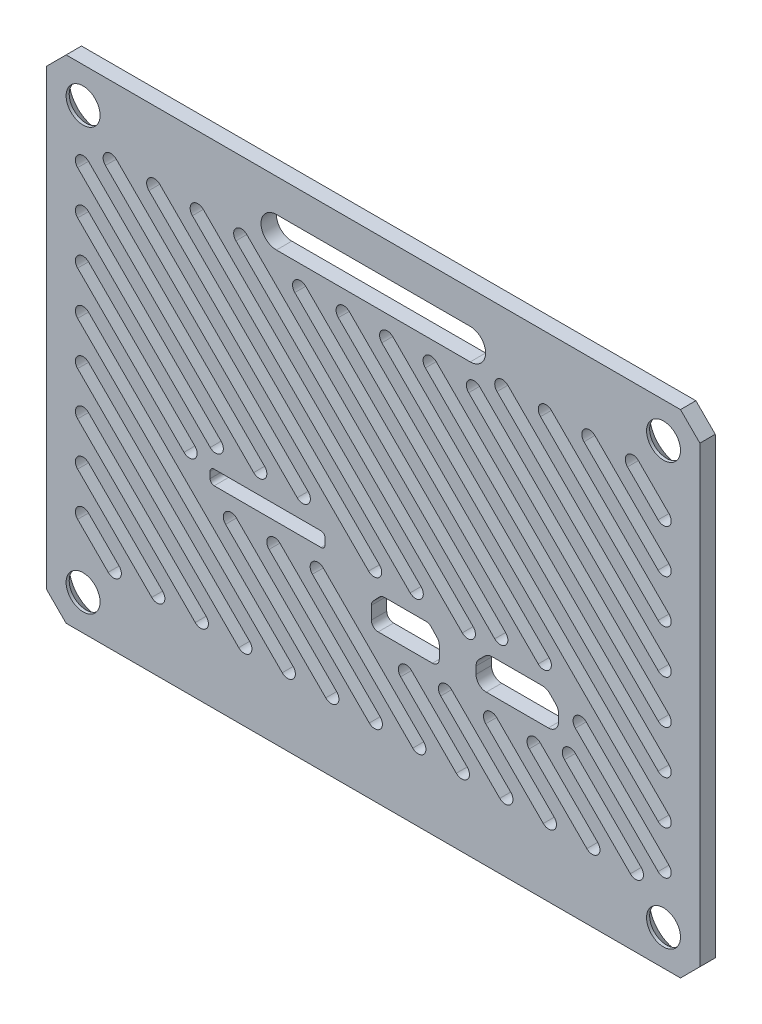
SolidWorks part; units mm, degrees
ref_plane "Front Plane" through (0, 0, 0) normal (0, 0, 1) x (1, 0, 0)
ref_plane "Top Plane" through (0, 0, 0) normal (0, 1, 0) x (1, 0, 0)
ref_plane "Right Plane" through (0, 0, 0) normal (1, 0, 0) x (0, 0, -1)
sketch "Sketch1" plane through (0, 0, 0) normal (0, 0, 1) x (1, 0, 0)
  line L1 (0, 0) -> (67.4, 0)
  line L2 (0, 0) -> (0, 50.8)
  line L3 (0, 50.8) -> (67.4, 50.8)
  line L4 (67.4, 0) -> (67.4, 50.8)
  dimension "D1" = 67.4
  dimension "D2" = 50.8
extrude "Boss-Extrude1" add sketch "Sketch1" along normal blind 1.5875
chamfer "Chamfer1" distance 2 angle 45 4 edges at (0, 0, 0.7937) (0, 50.8, 0.7937) (67.4, 0, 0.7937) (67.4, 50.8, 0.7937)
sketch "Sketch3" plane through (0, 0, 0) normal (0, 0, -1) x (-1, 0, 0)
  line L0 (-67.4, 25.4) -> (0, 25.4) construction
  line L1 (-67.4, 2) -> (-67.4, 48.8) construction
  line L2 (0, 48.8) -> (0, 2) construction
  line L3 (-63.65, 47.15) -> (-3.75, 47.15) construction
  line L4 (-65.4, 50.8) -> (-2, 50.8) construction
  line L5 (-33.7, 50.8) -> (-33.7, 0) construction
  line L6 (-2, 0) -> (-65.4, 0) construction
  line L7 (-3.75, 47.15) -> (-3.75, 3.65) construction
  circle A0 centre (-63.65, 47.15) radius 1.75
  circle A1 centre (-3.75, 47.15) radius 1.75
  circle A2 centre (-3.75, 3.65) radius 1.75
  circle A3 centre (-63.65, 3.65) radius 1.75
  arc A4 (-64.525, 4.6114) -> (-62.775, 4.6114) centre (-63.65, 3.65) ccw construction
  point P20 (-33.7, 47.15)
  point P21 (-3.75, 25.4)
  dimension "D1" = 3.5
extrude "Cut-Extrude2" cut sketch "Sketch3" against normal through all
chamfer "Chamfer2" distance 1.27 angle 45 4 edges at (2, 3.65, 0) (61.9, 3.65, 0) (2, 47.15, 0) (61.9, 47.15, 0)
sketch "Sketch5" plane through (0, 0, 0) normal (0, 0, -1) x (-1, 0, 0)
  line L0 (-43.7, 45.8) -> (-23.7, 45.8) construction
  line L1 (-43.7, 47.3875) -> (-23.7, 47.3875)
  line L2 (-43.7, 44.2125) -> (-23.7, 44.2125)
  line L3 (-33.7, 50.8) -> (-33.7, 45.8) construction
  line L5 (-65.4, 50.8) -> (-2, 50.8) construction
  arc A0 (-43.7, 47.3875) -> (-43.7, 44.2125) centre (-43.7, 45.8) ccw
  arc A1 (-23.7, 44.2125) -> (-23.7, 47.3875) centre (-23.7, 45.8) ccw
  point P2 (-33.7, 45.8)
  dimension "D1" = 1.5875
  dimension "D2" = 20
  dimension "D3" = 5
extrude "Cut-Extrude4" cut sketch "Sketch5" against normal through all
sketch "Sketch6" plane through (0, 0, 0) normal (0, 0, -1) x (-1, 0, 0)
  line L0 (-45.3591, 16.0375) -> (-51.7591, 16.0375) construction
  line L1 (-18.2758, 20.1823) -> (-21.3912, 20.1823) construction
  line L2 (-44.8091, 17.2375) -> (-44.8091, 16.6375) construction
  line L3 (-19.2565, 21.1623) -> (-19.4565, 21.1623) construction
  line L4 (-44.9701, 17.7229) -> (-45.5737, 18.3264) construction
  line L5 (-17.1065, 20.2823) -> (-17.1065, 21.2773) construction
  line L6 (-28.4665, 21.0123) -> (-28.4665, 20.2223) construction
  line L7 (-52.3091, 16.6375) -> (-52.3091, 16.5875) construction
  line L8 (-17.2765, 19.9283) -> (-28.2965, 19.9283)
  line L9 (-28.7205, 20.3523) -> (-28.7205, 20.9923)
  line L10 (-51.5444, 18.3264) -> (-52.148, 17.7229) construction
  line L11 (-17.2765, 21.4163) -> (-28.2965, 21.4163)
  line L12 (-51.0591, 18.4875) -> (-48.5691, 18.4875) construction
  line L13 (-45.3591, 16.0375) -> (-51.7591, 16.0375) construction
  line L14 (-45.3591, 15.5295) -> (-51.7591, 15.5295)
  line L15 (-44.8091, 17.3339) -> (-44.8091, 16.5875) construction
  line L16 (-52.8171, 17.3339) -> (-52.8171, 16.5875)
  line L17 (-44.9701, 17.7229) -> (-45.5737, 18.3264) construction
  line L18 (-51.9036, 18.6856) -> (-52.5072, 18.0821)
  line L19 (-51.1555, 18.9955) -> (-45.9626, 18.9955)
  line L20 (-52.3091, 17.3339) -> (-52.3091, 16.5875) construction
  line L21 (-44.6109, 18.0821) -> (-45.2145, 18.6856)
  line L22 (-44.3011, 17.3339) -> (-44.3011, 16.5875)
  line L23 (-51.5444, 18.3264) -> (-52.148, 17.7229) construction
  line L24 (-16.8525, 20.3523) -> (-16.8525, 20.9923)
  line L25 (-51.1555, 18.4875) -> (-45.9626, 18.4875) construction
  line L39 (-34.2021, 15.5875) -> (-39.8021, 15.5875) construction
  line L40 (-33.7521, 17.3577) -> (-33.7521, 16.0375) construction
  line L41 (-34.52, 18.3471) -> (-33.8755, 17.6673) construction
  line L42 (-36.8421, 18.4875) -> (-34.8466, 18.4875) construction
  line L43 (-40.2521, 16.0375) -> (-40.2521, 17.3577) construction
  line L44 (-40.1286, 17.6673) -> (-39.4841, 18.3471) construction
  line L45 (-39.1576, 18.4875) -> (-37.1621, 18.4875) construction
  line L46 (-34.2021, 15.5875) -> (-39.8021, 15.5875) construction
  line L47 (-33.7521, 17.3577) -> (-33.7521, 16.0375) construction
  line L48 (-34.52, 18.3471) -> (-33.8755, 17.6673) construction
  line L49 (-36.8421, 18.4875) -> (-34.8466, 18.4875) construction
  line L50 (-40.2521, 16.0375) -> (-40.2521, 17.3577) construction
  line L51 (-40.1286, 17.6673) -> (-39.4841, 18.3471) construction
  line L52 (-39.1576, 18.4875) -> (-37.1621, 18.4875) construction
  line L53 (-36.8421, 18.4875) -> (-37.1621, 18.4875) construction
  line L54 (-34.2021, 15.3335) -> (-39.8021, 15.3335)
  line L55 (-40.5061, 16.0375) -> (-40.5061, 17.3577)
  line L56 (-40.313, 17.8421) -> (-39.6685, 18.5219)
  line L57 (-39.1576, 18.7415) -> (-37.1621, 18.7415)
  line L58 (-36.8421, 18.7415) -> (-37.1621, 18.7415)
  line L59 (-36.8421, 18.7415) -> (-34.8466, 18.7415)
  line L60 (-34.3357, 18.5219) -> (-33.6912, 17.8421)
  line L61 (-33.4981, 17.3577) -> (-33.4981, 16.0375)
  line L193 (-17.1065, 20.3523) -> (-17.1065, 20.9923) construction
  line L195 (-17.2765, 20.1823) -> (-28.2965, 20.1823) construction
  line L199 (-28.4665, 20.3523) -> (-28.4665, 20.9923) construction
  line L200 (-17.2765, 21.1623) -> (-28.2965, 21.1623) construction
  arc A0 (-45.3591, 16.0375) -> (-44.8091, 16.5875) centre (-45.3591, 16.5875) ccw construction
  arc A1 (-44.8091, 17.3339) -> (-44.9701, 17.7229) centre (-45.3591, 17.3339) ccw construction
  arc A2 (-45.5737, 18.3264) -> (-45.9626, 18.4875) centre (-45.9626, 17.9375) ccw construction
  arc A3 (-52.3091, 16.5875) -> (-51.7591, 16.0375) centre (-51.7591, 16.5875) ccw construction
  arc A4 (-52.148, 17.7229) -> (-52.3091, 17.3339) centre (-51.7591, 17.3339) ccw construction
  arc A5 (-51.1555, 18.4875) -> (-51.5444, 18.3264) centre (-51.1555, 17.9375) ccw construction
  arc A6 (-45.3591, 16.0375) -> (-44.8091, 16.5875) centre (-45.3591, 16.5875) ccw construction
  arc A7 (-44.8091, 17.3339) -> (-44.9701, 17.7229) centre (-45.3591, 17.3339) ccw construction
  arc A8 (-45.5737, 18.3264) -> (-45.9626, 18.4875) centre (-45.9626, 17.9375) ccw construction
  arc A9 (-52.3091, 16.5875) -> (-51.7591, 16.0375) centre (-51.7591, 16.5875) ccw construction
  arc A10 (-52.148, 17.7229) -> (-52.3091, 17.3339) centre (-51.7591, 17.3339) ccw construction
  arc A11 (-51.1555, 18.4875) -> (-51.5444, 18.3264) centre (-51.1555, 17.9375) ccw construction
  arc A12 (-52.8171, 16.5875) -> (-51.7591, 15.5295) centre (-51.7591, 16.5875) ccw
  arc A13 (-52.5072, 18.0821) -> (-52.8171, 17.3339) centre (-51.7591, 17.3339) ccw
  arc A14 (-51.1555, 18.9955) -> (-51.9036, 18.6856) centre (-51.1555, 17.9375) ccw
  arc A15 (-45.2145, 18.6856) -> (-45.9626, 18.9955) centre (-45.9626, 17.9375) ccw
  arc A16 (-44.3011, 17.3339) -> (-44.6109, 18.0821) centre (-45.3591, 17.3339) ccw
  arc A17 (-45.3591, 15.5295) -> (-44.3011, 16.5875) centre (-45.3591, 16.5875) ccw
  arc A18 (-34.2021, 15.5875) -> (-33.7521, 16.0375) centre (-34.2021, 16.0375) ccw construction
  arc A19 (-33.7521, 17.3577) -> (-33.8755, 17.6673) centre (-34.2021, 17.3577) ccw construction
  arc A20 (-34.52, 18.3471) -> (-34.8466, 18.4875) centre (-34.8466, 18.0375) ccw construction
  arc A21 (-40.2521, 16.0375) -> (-39.8021, 15.5875) centre (-39.8021, 16.0375) ccw construction
  arc A22 (-40.1286, 17.6673) -> (-40.2521, 17.3577) centre (-39.8021, 17.3577) ccw construction
  arc A23 (-39.1576, 18.4875) -> (-39.4841, 18.3471) centre (-39.1576, 18.0375) ccw construction
  arc A24 (-34.2021, 15.5875) -> (-33.7521, 16.0375) centre (-34.2021, 16.0375) ccw construction
  arc A25 (-33.7521, 17.3577) -> (-33.8755, 17.6673) centre (-34.2021, 17.3577) ccw construction
  arc A26 (-34.52, 18.3471) -> (-34.8466, 18.4875) centre (-34.8466, 18.0375) ccw construction
  arc A27 (-40.2521, 16.0375) -> (-39.8021, 15.5875) centre (-39.8021, 16.0375) ccw construction
  arc A28 (-40.1286, 17.6673) -> (-40.2521, 17.3577) centre (-39.8021, 17.3577) ccw construction
  arc A29 (-39.1576, 18.4875) -> (-39.4841, 18.3471) centre (-39.1576, 18.0375) ccw construction
  arc A30 (-40.5061, 16.0375) -> (-39.8021, 15.3335) centre (-39.8021, 16.0375) ccw
  arc A31 (-40.313, 17.8421) -> (-40.5061, 17.3577) centre (-39.8021, 17.3577) ccw
  arc A32 (-39.1576, 18.7415) -> (-39.6685, 18.5219) centre (-39.1576, 18.0375) ccw
  arc A33 (-34.3357, 18.5219) -> (-34.8466, 18.7415) centre (-34.8466, 18.0375) ccw
  arc A34 (-33.4981, 17.3577) -> (-33.6912, 17.8421) centre (-34.2021, 17.3577) ccw
  arc A35 (-34.2021, 15.3335) -> (-33.4981, 16.0375) centre (-34.2021, 16.0375) ccw
  arc A36 (-28.7205, 20.3523) -> (-28.2965, 19.9283) centre (-28.2965, 20.3523) ccw
  arc A37 (-28.7205, 20.9923) -> (-28.2965, 21.4163) centre (-28.2965, 20.9923) cw
  arc A38 (-16.8525, 20.9923) -> (-17.2765, 21.4163) centre (-17.2765, 20.9923) ccw
  arc A39 (-17.2765, 19.9283) -> (-16.8525, 20.3523) centre (-17.2765, 20.3523) ccw
  arc A56 (-28.4665, 20.9923) -> (-28.2965, 21.1623) centre (-28.2965, 20.9923) cw construction
  arc A57 (-28.4665, 20.3523) -> (-28.2965, 20.1823) centre (-28.2965, 20.3523) ccw construction
  arc A58 (-17.1065, 20.9923) -> (-17.2765, 21.1623) centre (-17.2765, 20.9923) ccw construction
  arc A59 (-17.2765, 20.1823) -> (-17.1065, 20.3523) centre (-17.2765, 20.3523) ccw construction
  dimension "D3" = 0.254
  dimension "D5" = 0.17
  dimension "D1" = 0.508
  dimension "D2" = 0.254
extrude "Cut-Extrude5" cut sketch "Sketch6" against normal up to surface (1.5875 mm away) up to face at (33.7, 45.8, 1.5875)
sketch "Sketch7" plane through (0, 0, 0) normal (0, 0, -1) x (-1, 0, 0)
  line L0 (-3.75, 14.9388) -> (-11.3951, 7.2938) construction
  line L1 (-3.1887, 14.3776) -> (-10.8338, 6.7325)
  line L2 (-4.3113, 15.5001) -> (-11.9564, 7.855)
  line L3 (-14.724, 21.9254) -> (-3.75, 32.8994) construction
  line L4 (-28.2965, 18.4283) -> (-17.2765, 18.4283) construction
  line L5 (-15.3525, 20.3523) -> (-15.3525, 20.9923) construction
  line L7 (-17.2765, 22.9163) -> (-28.2965, 22.9163) construction
  line L8 (-30.2205, 20.9923) -> (-30.2205, 20.3523) construction
  line L9 (-28.2965, 19.9283) -> (-17.2765, 19.9283)
  line L10 (-2.9562, 6.5) -> (-64.4437, 6.5) construction
  line L11 (-2.9562, 6.5) -> (-2.9562, 44.3) construction
  line L12 (-2.9562, 44.3) -> (-64.4437, 44.3) construction
  line L13 (-64.4437, 6.5) -> (-64.4437, 44.3) construction
  line L14 (-60.8864, 44.3) -> (-50.65, 44.3) construction
  line L16 (-6.5136, 6.5) -> (-60.8864, 6.5) construction
  line L17 (-3.75, 10.4487) -> (-6.905, 7.2938) construction
  line L18 (-3.1887, 9.8875) -> (-6.3437, 6.7325)
  line L19 (-4.3113, 11.01) -> (-7.4662, 7.855)
  line L20 (-3.75, 19.429) -> (-15.8852, 7.2938) construction
  line L21 (-3.1887, 18.8677) -> (-15.324, 6.7325)
  line L22 (-4.3113, 19.9902) -> (-16.4465, 7.855)
  line L23 (-3.75, 23.9191) -> (-20.3754, 7.2938) construction
  line L24 (-3.1887, 23.3578) -> (-19.8141, 6.7325)
  line L25 (-4.3113, 24.4804) -> (-20.9366, 7.855)
  line L26 (-3.75, 28.4092) -> (-24.8655, 7.2938) construction
  line L27 (-3.1887, 27.848) -> (-24.3042, 6.7325)
  line L28 (-4.3113, 28.9705) -> (-25.4267, 7.855)
  line L29 (-19.0148, 17.6345) -> (-29.3556, 7.2938) construction
  line L30 (-18.4535, 17.0733) -> (-28.7943, 6.7325)
  line L31 (-19.5761, 18.1958) -> (-29.9169, 7.855)
  line L32 (-23.5049, 17.6345) -> (-33.8457, 7.2938) construction
  line L33 (-22.9437, 17.0733) -> (-33.2845, 6.7325)
  line L34 (-24.0662, 18.1958) -> (-34.407, 7.855)
  line L35 (-27.9761, 17.6535) -> (-38.3359, 7.2938) construction
  line L36 (-27.4148, 17.0922) -> (-37.7746, 6.7325)
  line L37 (-28.5374, 18.2148) -> (-38.8971, 7.855)
  line L38 (-3.75, 41.8796) -> (-21.9196, 23.71) construction
  line L39 (-3.1887, 41.3183) -> (-21.3583, 23.1488)
  line L40 (-4.3113, 42.4409) -> (-22.4808, 24.2713)
  line L41 (-37.08, 13.0397) -> (-42.826, 7.2938) construction
  line L42 (-36.5187, 12.4785) -> (-42.2647, 6.7325)
  line L43 (-37.6413, 13.601) -> (-43.3873, 7.855)
  line L44 (-6.6135, 43.5063) -> (-26.4097, 23.71) construction
  line L45 (-6.0522, 42.945) -> (-25.8484, 23.1488)
  line L46 (-7.1748, 44.0675) -> (-26.971, 24.2713)
  line L47 (-41.2158, 13.3941) -> (-47.3161, 7.2938) construction
  line L48 (-40.6546, 12.8328) -> (-46.7549, 6.7325)
  line L49 (-41.7771, 13.9553) -> (-47.8774, 7.855)
  line L50 (-45.8643, 13.2357) -> (-51.8062, 7.2938) construction
  line L51 (-45.303, 12.6745) -> (-51.245, 6.7325)
  line L52 (-46.4255, 13.797) -> (-52.3675, 7.855)
  line L53 (-11.1036, 43.5063) -> (-33.7733, 20.8365) construction
  line L54 (-10.5424, 42.945) -> (-33.2121, 20.2753)
  line L55 (-11.6649, 44.0675) -> (-34.3346, 21.3978)
  line L56 (-15.5937, 43.5063) -> (-38.0647, 21.0352) construction
  line L57 (-15.0325, 42.945) -> (-37.5035, 20.474)
  line L58 (-16.155, 44.0675) -> (-38.626, 21.5965)
  line L59 (-50.3544, 13.2357) -> (-56.2964, 7.2938) construction
  line L60 (-49.7931, 12.6745) -> (-55.7351, 6.7325)
  line L61 (-50.9156, 13.797) -> (-56.8576, 7.855)
  line L62 (-53.9922, 14.088) -> (-60.7865, 7.2938) construction
  line L63 (-53.4309, 13.5268) -> (-60.2252, 6.7325)
  line L64 (-54.5535, 14.6493) -> (-61.3478, 7.855)
  line L65 (-20.0839, 43.5063) -> (-43.4426, 20.1475) construction
  line L66 (-19.5226, 42.945) -> (-42.8814, 19.5862)
  line L67 (-20.6451, 44.0675) -> (-44.0039, 20.7087)
  line L68 (-26.1615, 41.9188) -> (-46.791, 21.2892) construction
  line L69 (-25.6002, 41.3575) -> (-46.2297, 20.728)
  line L70 (-26.7228, 42.48) -> (-47.3523, 21.8505)
  line L71 (-55.1084, 17.462) -> (-63.65, 8.9204) construction
  line L72 (-54.5471, 16.9008) -> (-63.0887, 8.3591)
  line L73 (-55.6696, 18.0233) -> (-64.2113, 9.4817)
  line L74 (-35.1418, 41.9188) -> (-63.65, 13.4105) construction
  line L75 (-34.5805, 41.3575) -> (-63.0887, 12.8492)
  line L76 (-35.703, 42.48) -> (-64.2113, 13.9718)
  line L77 (-28.7205, 20.9923) -> (-28.7205, 20.3523)
  line L78 (-5.3275, 8.8712) -> (-7.5725, 11.1163) construction
  line L79 (-7.5725, 11.1163) -> (-9.8176, 13.3614) construction
  line L80 (-9.8176, 13.3614) -> (-12.0627, 15.6064) construction
  line L81 (-12.0627, 15.6064) -> (-14.3077, 17.8515) construction
  line L82 (-15.2852, 22.4867) -> (-4.3113, 33.4606)
  line L83 (-14.1627, 21.3641) -> (-3.1887, 32.3381)
  line L84 (-17.2765, 21.4163) -> (-28.2965, 21.4163)
  line L85 (-16.8525, 20.3523) -> (-16.8525, 20.9923)
  line L86 (-28.2965, 19.9283) -> (-17.2765, 19.9283) construction
  line L87 (-28.7205, 20.9923) -> (-28.7205, 20.3523) construction
  line L88 (-17.2765, 21.4163) -> (-28.2965, 21.4163) construction
  line L89 (-16.8525, 20.3523) -> (-16.8525, 20.9923) construction
  line L90 (-3.75, 37.3895) -> (-17.4294, 23.71) construction
  line L91 (-3.1887, 36.8282) -> (-16.8682, 23.1488)
  line L92 (-4.3113, 37.9508) -> (-17.9907, 24.2713)
  line L93 (-38.3359, 7.2938) -> (-40.5809, 9.5388) construction
  line L94 (-47.3161, 7.2938) -> (-49.5612, 9.5388) construction
  line L95 (-51.8062, 7.2938) -> (-54.0513, 9.5388) construction
  line L96 (-56.2964, 7.2938) -> (-58.5414, 9.5388) construction
  line L97 (-5.3275, 8.8712) -> (-2.9562, 6.5) construction
  line L99 (-60.7865, 7.2938) -> (-63.0316, 9.5388) construction
  line L100 (-42.826, 7.2938) -> (-45.0711, 9.5388) construction
  line L101 (-33.8457, 7.2938) -> (-36.0908, 9.5388) construction
  line L102 (-29.3556, 7.2938) -> (-31.6007, 9.5388) construction
  line L103 (-23.7, 48.8875) -> (-43.7, 48.8875)
  line L104 (-43.7, 42.7125) -> (-23.7, 42.7125)
  line L105 (-23.7, 48.8875) -> (-43.7, 48.8875) construction
  line L106 (-43.7, 42.7125) -> (-23.7, 42.7125) construction
  line L107 (-34.8466, 20.2415) -> (-39.1576, 20.2415)
  line L108 (-40.757, 19.5539) -> (-41.4015, 18.8741)
  line L109 (-42.0061, 17.3577) -> (-42.0061, 16.0375)
  line L110 (-39.8021, 13.8335) -> (-34.2021, 13.8335)
  line L111 (-31.9981, 16.0375) -> (-31.9981, 17.3577)
  line L112 (-32.6026, 18.8741) -> (-33.2471, 19.5539)
  line L113 (-34.8466, 20.2415) -> (-39.1576, 20.2415) construction
  line L114 (-40.757, 19.5539) -> (-41.4015, 18.8741) construction
  line L115 (-42.0061, 17.3577) -> (-42.0061, 16.0375) construction
  line L116 (-39.8021, 13.8335) -> (-34.2021, 13.8335) construction
  line L117 (-31.9981, 16.0375) -> (-31.9981, 17.3577) construction
  line L118 (-32.6026, 18.8741) -> (-33.2471, 19.5539) construction
  line L119 (-42.8011, 16.5875) -> (-42.8011, 17.3339)
  line L120 (-43.5503, 19.1427) -> (-44.1538, 19.7463)
  line L121 (-45.9626, 20.4955) -> (-51.1555, 20.4955)
  line L122 (-52.9643, 19.7463) -> (-53.5678, 19.1427)
  line L123 (-54.3171, 17.3339) -> (-54.3171, 16.5875)
  line L124 (-51.7591, 14.0295) -> (-45.3591, 14.0295)
  line L125 (-42.8011, 16.5875) -> (-42.8011, 17.3339) construction
  line L126 (-43.5503, 19.1427) -> (-44.1538, 19.7463) construction
  line L127 (-45.9626, 20.4955) -> (-51.1555, 20.4955) construction
  line L128 (-52.9643, 19.7463) -> (-53.5678, 19.1427) construction
  line L129 (-54.3171, 17.3339) -> (-54.3171, 16.5875) construction
  line L130 (-51.7591, 14.0295) -> (-45.3591, 14.0295) construction
  line L131 (-24.8655, 7.2938) -> (-27.1105, 9.5388) construction
  line L132 (-63.65, 13.4105) -> (-61.4049, 11.1654) construction
  line L133 (-39.6319, 41.9188) -> (-63.65, 17.9006) construction
  line L134 (-39.0706, 41.3575) -> (-63.0887, 17.3394)
  line L135 (-40.1932, 42.48) -> (-64.2113, 18.4619)
  line L136 (-63.65, 17.9006) -> (-61.4049, 15.6556) construction
  line L137 (-44.1012, 41.9395) -> (-63.65, 22.3908) construction
  line L138 (-43.54, 41.3783) -> (-63.0887, 21.8295)
  line L139 (-44.6625, 42.5008) -> (-64.2113, 22.952)
  line L140 (-47.0246, 43.5063) -> (-63.65, 26.8809) construction
  line L141 (-46.4634, 42.945) -> (-63.0887, 26.3196)
  line L142 (-47.5859, 44.0675) -> (-64.2113, 27.4422)
  line L143 (-51.5148, 43.5063) -> (-63.65, 31.371) construction
  line L144 (-50.9535, 42.945) -> (-63.0887, 30.8098)
  line L145 (-52.076, 44.0675) -> (-64.2113, 31.9323)
  line L146 (-56.0049, 43.5063) -> (-63.65, 35.8612) construction
  line L147 (-55.4436, 42.945) -> (-63.0887, 35.2999)
  line L148 (-56.5662, 44.0675) -> (-64.2113, 36.4224)
  line L149 (-63.65, 22.3908) -> (-61.4049, 20.1457) construction
  line L150 (-63.65, 26.8809) -> (-61.4049, 24.6358) construction
  line L151 (-63.65, 31.371) -> (-61.4049, 29.126) construction
  line L152 (-63.65, 35.8612) -> (-61.4049, 33.6161) construction
  line L153 (-60.495, 43.5063) -> (-63.65, 40.3513) construction
  line L154 (-59.9338, 42.945) -> (-63.0887, 39.79)
  line L155 (-61.0563, 44.0675) -> (-64.2113, 40.9125)
  line L156 (-63.65, 40.3513) -> (-61.4049, 38.1062) construction
  line L157 (-30.6516, 41.9188) -> (-51.2811, 21.2892) construction
  line L158 (-30.0904, 41.3575) -> (-50.7199, 20.728)
  line L159 (-31.2129, 42.48) -> (-51.8424, 21.8505)
  line L161 (-64.4437, 44.3) -> (-62.0725, 41.9288) construction
  arc A1 (-3.1887, 14.3776) -> (-4.3113, 15.5001) centre (-3.75, 14.9388) ccw
  arc A2 (-3.1887, 9.8875) -> (-4.3113, 11.01) centre (-3.75, 10.4487) ccw
  arc A3 (-7.4662, 7.855) -> (-6.3437, 6.7325) centre (-6.905, 7.2938) ccw
  arc A4 (-11.9564, 7.855) -> (-10.8338, 6.7325) centre (-11.3951, 7.2938) ccw
  arc A5 (-3.1887, 18.8677) -> (-4.3113, 19.9902) centre (-3.75, 19.429) ccw
  arc A6 (-16.4465, 7.855) -> (-15.324, 6.7325) centre (-15.8852, 7.2938) ccw
  arc A7 (-3.1887, 23.3578) -> (-4.3113, 24.4804) centre (-3.75, 23.9191) ccw
  arc A8 (-20.9366, 7.855) -> (-19.8141, 6.7325) centre (-20.3754, 7.2938) ccw
  arc A9 (-3.1887, 27.848) -> (-4.3113, 28.9705) centre (-3.75, 28.4092) ccw
  arc A10 (-25.4267, 7.855) -> (-24.3042, 6.7325) centre (-24.8655, 7.2938) ccw
  arc A11 (-18.4535, 17.0733) -> (-19.5761, 18.1958) centre (-19.0148, 17.6345) ccw
  arc A12 (-29.9169, 7.855) -> (-28.7943, 6.7325) centre (-29.3556, 7.2938) ccw
  arc A13 (-22.9437, 17.0733) -> (-24.0662, 18.1958) centre (-23.5049, 17.6345) ccw
  arc A14 (-34.407, 7.855) -> (-33.2845, 6.7325) centre (-33.8457, 7.2938) ccw
  arc A15 (-27.4148, 17.0922) -> (-28.5374, 18.2148) centre (-27.9761, 17.6535) ccw
  arc A16 (-38.8971, 7.855) -> (-37.7746, 6.7325) centre (-38.3359, 7.2938) ccw
  arc A17 (-3.1887, 41.3183) -> (-4.3113, 42.4409) centre (-3.75, 41.8796) ccw
  arc A18 (-22.4808, 24.2713) -> (-21.3583, 23.1488) centre (-21.9196, 23.71) ccw
  arc A19 (-36.5187, 12.4785) -> (-37.6413, 13.601) centre (-37.08, 13.0397) ccw
  arc A20 (-43.3873, 7.855) -> (-42.2647, 6.7325) centre (-42.826, 7.2938) ccw
  arc A21 (-6.0522, 42.945) -> (-7.1748, 44.0675) centre (-6.6135, 43.5063) ccw
  arc A22 (-26.971, 24.2713) -> (-25.8484, 23.1488) centre (-26.4097, 23.71) ccw
  arc A23 (-40.6546, 12.8328) -> (-41.7771, 13.9553) centre (-41.2158, 13.3941) ccw
  arc A24 (-47.8774, 7.855) -> (-46.7549, 6.7325) centre (-47.3161, 7.2938) ccw
  arc A25 (-45.303, 12.6745) -> (-46.4255, 13.797) centre (-45.8643, 13.2357) ccw
  arc A26 (-52.3675, 7.855) -> (-51.245, 6.7325) centre (-51.8062, 7.2938) ccw
  arc A27 (-10.5424, 42.945) -> (-11.6649, 44.0675) centre (-11.1036, 43.5063) ccw
  arc A28 (-34.3346, 21.3978) -> (-33.2121, 20.2753) centre (-33.7733, 20.8365) ccw
  arc A29 (-15.0325, 42.945) -> (-16.155, 44.0675) centre (-15.5937, 43.5063) ccw
  arc A30 (-38.626, 21.5965) -> (-37.5035, 20.474) centre (-38.0647, 21.0352) ccw
  arc A31 (-49.7931, 12.6745) -> (-50.9156, 13.797) centre (-50.3544, 13.2357) ccw
  arc A32 (-56.8576, 7.855) -> (-55.7351, 6.7325) centre (-56.2964, 7.2938) ccw
  arc A33 (-53.4309, 13.5268) -> (-54.5535, 14.6493) centre (-53.9922, 14.088) ccw
  arc A34 (-61.3478, 7.855) -> (-60.2252, 6.7325) centre (-60.7865, 7.2938) ccw
  arc A35 (-19.5226, 42.945) -> (-20.6451, 44.0675) centre (-20.0839, 43.5063) ccw
  arc A36 (-44.0039, 20.7087) -> (-42.8814, 19.5862) centre (-43.4426, 20.1475) ccw
  arc A37 (-25.6002, 41.3575) -> (-26.7228, 42.48) centre (-26.1615, 41.9188) ccw
  arc A38 (-47.3523, 21.8505) -> (-46.2297, 20.728) centre (-46.791, 21.2892) ccw
  arc A39 (-54.5471, 16.9008) -> (-55.6696, 18.0233) centre (-55.1084, 17.462) ccw
  arc A40 (-64.2113, 9.4817) -> (-63.0887, 8.3591) centre (-63.65, 8.9204) ccw
  arc A41 (-34.5805, 41.3575) -> (-35.703, 42.48) centre (-35.1418, 41.9188) ccw
  arc A42 (-64.2113, 13.9718) -> (-63.0887, 12.8492) centre (-63.65, 13.4105) ccw
  arc A43 (-17.2765, 18.4283) -> (-15.3525, 20.3523) centre (-17.2765, 20.3523) ccw construction
  arc A44 (-15.3525, 20.9923) -> (-17.2765, 22.9163) centre (-17.2765, 20.9923) ccw construction
  arc A45 (-28.2965, 22.9163) -> (-30.2205, 20.9923) centre (-28.2965, 20.9923) ccw construction
  arc A46 (-30.2205, 20.3523) -> (-28.2965, 18.4283) centre (-28.2965, 20.3523) ccw construction
  arc A47 (-17.2765, 19.9283) -> (-16.8525, 20.3523) centre (-17.2765, 20.3523) ccw
  arc A48 (-28.7205, 20.3523) -> (-28.2965, 19.9283) centre (-28.2965, 20.3523) ccw
  arc A49 (-28.2965, 21.4163) -> (-28.7205, 20.9923) centre (-28.2965, 20.9923) ccw
  arc A50 (-16.8525, 20.9923) -> (-17.2765, 21.4163) centre (-17.2765, 20.9923) ccw
  arc A51 (-17.2765, 19.9283) -> (-16.8525, 20.3523) centre (-17.2765, 20.3523) ccw construction
  arc A52 (-28.7205, 20.3523) -> (-28.2965, 19.9283) centre (-28.2965, 20.3523) ccw construction
  arc A53 (-28.2965, 21.4163) -> (-28.7205, 20.9923) centre (-28.2965, 20.9923) ccw construction
  arc A54 (-16.8525, 20.9923) -> (-17.2765, 21.4163) centre (-17.2765, 20.9923) ccw construction
  arc A55 (-15.2852, 22.4867) -> (-14.1627, 21.3641) centre (-14.724, 21.9254) ccw
  arc A56 (-3.1887, 32.3381) -> (-4.3113, 33.4606) centre (-3.75, 32.8994) ccw
  arc A57 (-3.1887, 36.8282) -> (-4.3113, 37.9508) centre (-3.75, 37.3895) ccw
  arc A58 (-17.9907, 24.2713) -> (-16.8682, 23.1488) centre (-17.4294, 23.71) ccw
  arc A62 (-39.0706, 41.3575) -> (-40.1932, 42.48) centre (-39.6319, 41.9188) ccw
  arc A63 (-43.7, 48.8875) -> (-43.7, 42.7125) centre (-43.7, 45.8) ccw
  arc A64 (-23.7, 42.7125) -> (-23.7, 48.8875) centre (-23.7, 45.8) ccw
  arc A65 (-43.7, 48.8875) -> (-43.7, 42.7125) centre (-43.7, 45.8) ccw construction
  arc A66 (-23.7, 42.7125) -> (-23.7, 48.8875) centre (-23.7, 45.8) ccw construction
  arc A67 (-64.2113, 18.4619) -> (-63.0887, 17.3394) centre (-63.65, 17.9006) ccw
  arc A68 (-43.54, 41.3783) -> (-44.6625, 42.5008) centre (-44.1012, 41.9395) ccw
  arc A69 (-64.2113, 22.952) -> (-63.0887, 21.8295) centre (-63.65, 22.3908) ccw
  arc A70 (-46.4634, 42.945) -> (-47.5859, 44.0675) centre (-47.0246, 43.5063) ccw
  arc A71 (-33.2471, 19.5539) -> (-34.8466, 20.2415) centre (-34.8466, 18.0375) ccw
  arc A72 (-39.1576, 20.2415) -> (-40.757, 19.5539) centre (-39.1576, 18.0375) ccw
  arc A73 (-41.4015, 18.8741) -> (-42.0061, 17.3577) centre (-39.8021, 17.3577) ccw
  arc A74 (-42.0061, 16.0375) -> (-39.8021, 13.8335) centre (-39.8021, 16.0375) ccw
  arc A75 (-34.2021, 13.8335) -> (-31.9981, 16.0375) centre (-34.2021, 16.0375) ccw
  arc A76 (-31.9981, 17.3577) -> (-32.6026, 18.8741) centre (-34.2021, 17.3577) ccw
  arc A77 (-33.2471, 19.5539) -> (-34.8466, 20.2415) centre (-34.8466, 18.0375) ccw construction
  arc A78 (-39.1576, 20.2415) -> (-40.757, 19.5539) centre (-39.1576, 18.0375) ccw construction
  arc A79 (-41.4015, 18.8741) -> (-42.0061, 17.3577) centre (-39.8021, 17.3577) ccw construction
  arc A80 (-42.0061, 16.0375) -> (-39.8021, 13.8335) centre (-39.8021, 16.0375) ccw construction
  arc A81 (-34.2021, 13.8335) -> (-31.9981, 16.0375) centre (-34.2021, 16.0375) ccw construction
  arc A82 (-31.9981, 17.3577) -> (-32.6026, 18.8741) centre (-34.2021, 17.3577) ccw construction
  arc A83 (-45.3591, 14.0295) -> (-42.8011, 16.5875) centre (-45.3591, 16.5875) ccw
  arc A84 (-42.8011, 17.3339) -> (-43.5503, 19.1427) centre (-45.3591, 17.3339) ccw
  arc A85 (-44.1538, 19.7463) -> (-45.9626, 20.4955) centre (-45.9626, 17.9375) ccw
  arc A86 (-51.1555, 20.4955) -> (-52.9643, 19.7463) centre (-51.1555, 17.9375) ccw
  arc A87 (-53.5678, 19.1427) -> (-54.3171, 17.3339) centre (-51.7591, 17.3339) ccw
  arc A88 (-54.3171, 16.5875) -> (-51.7591, 14.0295) centre (-51.7591, 16.5875) ccw
  arc A89 (-45.3591, 14.0295) -> (-42.8011, 16.5875) centre (-45.3591, 16.5875) ccw construction
  arc A90 (-42.8011, 17.3339) -> (-43.5503, 19.1427) centre (-45.3591, 17.3339) ccw construction
  arc A91 (-44.1538, 19.7463) -> (-45.9626, 20.4955) centre (-45.9626, 17.9375) ccw construction
  arc A92 (-51.1555, 20.4955) -> (-52.9643, 19.7463) centre (-51.1555, 17.9375) ccw construction
  arc A93 (-53.5678, 19.1427) -> (-54.3171, 17.3339) centre (-51.7591, 17.3339) ccw construction
  arc A94 (-54.3171, 16.5875) -> (-51.7591, 14.0295) centre (-51.7591, 16.5875) ccw construction
  arc A95 (-64.2113, 27.4422) -> (-63.0887, 26.3196) centre (-63.65, 26.8809) ccw
  arc A96 (-50.9535, 42.945) -> (-52.076, 44.0675) centre (-51.5148, 43.5063) ccw
  arc A97 (-64.2113, 31.9323) -> (-63.0887, 30.8098) centre (-63.65, 31.371) ccw
  arc A98 (-55.4436, 42.945) -> (-56.5662, 44.0675) centre (-56.0049, 43.5063) ccw
  arc A99 (-64.2113, 36.4224) -> (-63.0887, 35.2999) centre (-63.65, 35.8612) ccw
  arc A100 (-59.9338, 42.945) -> (-61.0563, 44.0675) centre (-60.495, 43.5063) ccw
  arc A101 (-64.2113, 40.9125) -> (-63.0887, 39.79) centre (-63.65, 40.3513) ccw
  arc A102 (-30.0904, 41.3575) -> (-31.2129, 42.48) centre (-30.6516, 41.9188) ccw
  arc A103 (-51.8424, 21.8505) -> (-50.7199, 20.728) centre (-51.2811, 21.2892) ccw
  point P5 (-7.5725, 11.1163)
  point P23 (-63.65, 47.15)
  point P33 (-5.3275, 8.8712)
  point P43 (-9.8176, 13.3614)
  point P50 (-12.0627, 15.6064)
  point P57 (-14.3077, 17.8515)
  point P64 (-24.1852, 12.4642)
  point P71 (-28.6753, 12.4642)
  point P78 (-33.156, 12.4736)
  point P85 (-12.8348, 32.7948)
  point P92 (-39.953, 10.1667)
  point P99 (-16.5116, 33.6081)
  point P106 (-44.266, 10.3439)
  point P113 (-48.8353, 10.2647)
  point P120 (-22.4385, 32.1714)
  point P127 (-26.8292, 32.2708)
  point P134 (-53.3254, 10.2647)
  point P141 (-57.3894, 10.6909)
  point P148 (-31.7633, 31.8269)
  point P155 (-36.4763, 31.604)
  point P162 (-59.3792, 13.1912)
  point P169 (-49.3959, 27.6646)
  point P179 (-9.237, 27.4124)
  point P199 (-10.5897, 30.5498)
  point P270 (-51.6409, 29.9097)
  point P280 (-53.8756, 32.1652)
  point P287 (-55.3373, 35.1936)
  point P294 (-57.5824, 37.4386)
  point P301 (-59.8275, 39.6837)
  point P316 (-62.0725, 41.9288)
  point P325 (-40.9664, 31.604)
  point P333 (-3.75, 3.65)
  dimension "D1" = 0.7937
  dimension "D2" = 45
  dimension "D4" = 3.175
  dimension "D5" = 0
  dimension "D10" = 1.5
  dimension "D6" = 1.5
  dimension "D9" = 1.5
  dimension "D11" = 1.5
extrude "Cut-Extrude6" cut sketch "Sketch7" against normal through all
